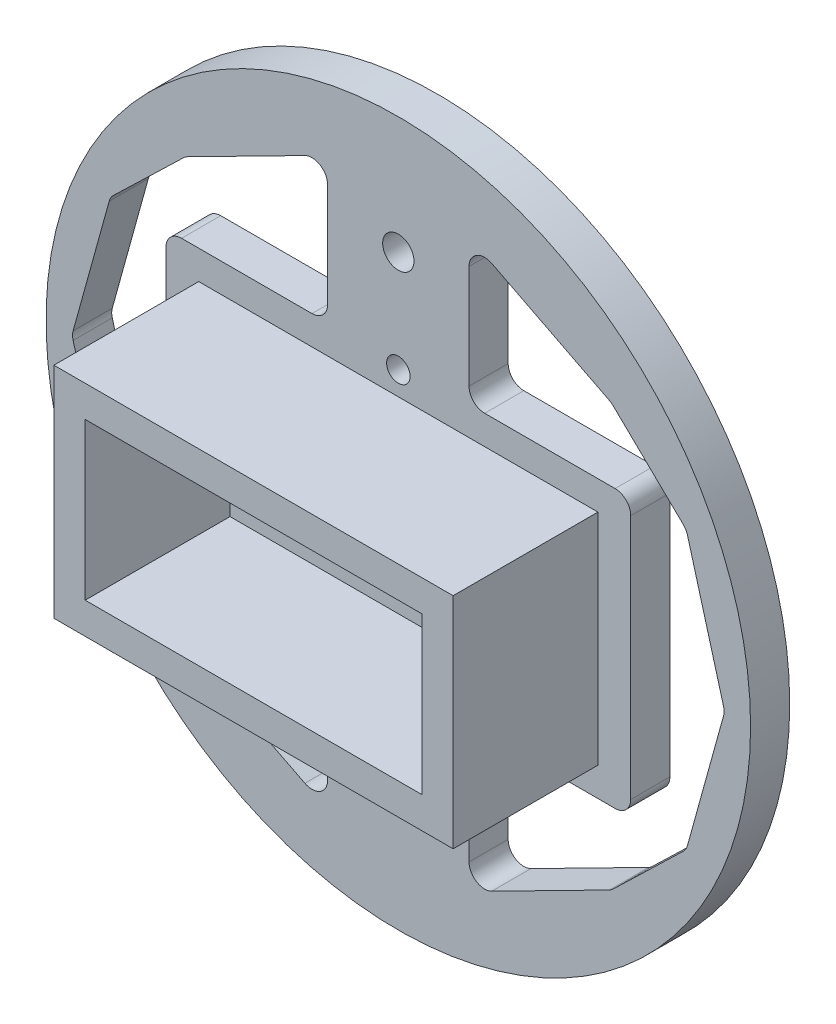
SolidWorks part; units mm, degrees
ref_plane "Front Plane" through (0, 0, 0) normal (0, 0, 1) x (1, 0, 0)
ref_plane "Top Plane" through (0, 0, 0) normal (0, 1, 0) x (1, 0, 0)
ref_plane "Right Plane" through (0, 0, 0) normal (1, 0, 0) x (0, 0, -1)
sketch "Sketch1" plane through (0, 0, 0) normal (0, 0, 1) x (1, 0, 0)
  line L0 (0, 57.2553) -> (0, -57.7928) construction
  line L1 (-56.6552, 0) -> (66.2483, 0) construction
  circle A0 centre (0, 0) radius 45
  circle A1 centre (0, 0) radius 2.5
  circle A2 centre (0, 17) radius 1.5
  circle A3 centre (17, 0) radius 1.5
  circle A4 centre (0, -17) radius 1.5
  circle A5 centre (-17, 0) radius 1.5
  point P19 (0, 0)
  dimension "D1" = 90
  dimension "D2" = 4
  dimension "D3" = 3
  dimension "D4" = 5
extrude "Boss-Extrude1" add sketch "Sketch1" along normal blind 5
sketch "Sketch2" plane through (0, 0, 5) normal (0, 0, 1) x (1, 0, 0)
  line L0 (0, 45) -> (0, -45) construction
  line L1 (-45, 0) -> (45, 0) construction
  line L4 (-25.5, 10) -> (-25.5, -10)
  line L6 (-21.5, 10) -> (-21.5, -10)
  line L7 (-21.5, 10) -> (0, 10)
  line L8 (-25.5, 10) -> (-25.5, 14)
  line L9 (-25.5, 14) -> (0, 14)
  line L10 (0, 10) -> (0, 14)
  line L11 (-21.5, -10) -> (0, -10)
  line L12 (-25.5, -10) -> (-25.5, -14)
  line L13 (-25.5, -14) -> (0, -14)
  line L14 (0, -10) -> (0, -14)
  circle A0 centre (0, 0) radius 45 construction
  circle A1 centre (0, -17) radius 1.5 construction
  point P11 (-25.5, 0)
  dimension "D1" = 21.5
  dimension "D2" = 4
  dimension "D3" = 20
  dimension "D4" = 25.5
extrude "Boss-Extrude2" add sketch "Sketch2" along normal blind 18.5
mirror "Mirror1" about plane through (0, 0, 0) normal (1, 0, 0) of "Boss-Extrude2"
sketch "Sketch4" plane through (0, 0, 5) normal (0, 0, 1) x (1, 0, 0)
  line L0 (-45, 0) -> (45, 0) construction
  circle A0 centre (0, 30) radius 2
  circle A1 centre (0, 0) radius 45 construction
  circle A2 centre (0, -30) radius 2
  dimension "D1" = 4
  dimension "D2" = 30
extrude "Cut-Extrude1" cut sketch "Sketch4" against normal blind 10
sketch "Sketch5" plane through (0, 0, 5) normal (0, 0, 1) x (1, 0, 0)
  line L0 (-29.6896, 17.695) -> (-9.0318, 17.695)
  line L1 (-9.0318, 17.695) -> (-9.0318, 36.201)
  line L2 (-9.0318, 36.201) -> (-27.215, 26.948)
  line L3 (-27.215, 26.948) -> (-36.7908, 17.695)
  line L4 (-36.7908, 17.695) -> (-41.6896, 0)
  line L5 (-41.6896, 0) -> (-29.6896, 0)
  line L6 (-29.6896, -17.695) -> (-29.6896, 17.695)
  line L7 (-12.6899, 0) -> (11.9488, 0) construction
  line L8 (0, 7.5813) -> (0, -6.5134) construction
  line L11 (25.5, 14) -> (25.5, -14) construction
  line L12 (-25.5, -14) -> (25.5, -14) construction
  line L13 (-36.7908, -17.695) -> (-41.6896, 0)
  line L14 (-27.215, -26.948) -> (-36.7908, -17.695)
  line L15 (-9.0318, -36.201) -> (-27.215, -26.948)
  line L16 (-9.0318, -17.695) -> (-9.0318, -36.201)
  line L17 (-29.6896, -17.695) -> (-9.0318, -17.695)
  line L18 (29.6896, -17.695) -> (9.0318, -17.695)
  line L19 (9.0318, -17.695) -> (9.0318, -36.201)
  line L20 (9.0318, -36.201) -> (27.215, -26.948)
  line L21 (27.215, -26.948) -> (36.7908, -17.695)
  line L22 (36.7908, -17.695) -> (41.6896, 0)
  line L23 (29.6896, -17.695) -> (29.6896, 17.695)
  line L24 (41.6896, 0) -> (29.6896, 0)
  line L25 (36.7908, 17.695) -> (41.6896, 0)
  line L26 (27.215, 26.948) -> (36.7908, 17.695)
  line L27 (9.0318, 36.201) -> (27.215, 26.948)
  line L28 (9.0318, 17.695) -> (9.0318, 36.201)
  line L29 (29.6896, 17.695) -> (9.0318, 17.695)
  dimension "D1" = 12
  dimension "D2" = 29.6896
  dimension "D3" = 34.5318
  dimension "D4" = 52.715
  dimension "D5" = 62.2908
  dimension "D6" = 28
  dimension "D7" = 31.695
  dimension "D8" = 40.948
  dimension "D9" = 50.201
extrude "Cut-Extrude2" cut sketch "Sketch5" against normal blind 10 contours L29 L23 L24 L25 L26 L27 L28 | L22 L24 L23 L18 L19 L20 L21 | L17 L6 L5 L13 L14 L15 L16 | L5 L6 L0 L1 L2 L3 L4
fillet "Fillet1" radius 2 22 edges at (29.6896, -17.695, 2.5) (9.0318, 36.201, 2.5) (9.0318, 17.695, 2.5) (29.6896, 17.695, 2.5) (27.215, 26.948, 2.5) (36.7908, 17.695, 2.5) (41.6896, 0, 2.5) (36.7908, -17.695, 2.5) (27.215, -26.948, 2.5) (9.0318, -36.201, 2.5) (9.0318, -17.695, 2.5) (-9.0318, -36.201, 2.5) (-9.0318, -17.695, 2.5) (-27.215, -26.948, 2.5) (-36.7908, -17.695, 2.5) (-29.6896, -17.695, 2.5) (-41.6896, 0, 2.5) (-36.7908, 17.695, 2.5) (-29.6896, 17.695, 2.5) (-9.0318, 17.695, 2.5) (-27.215, 26.948, 2.5) (-9.0318, 36.201, 2.5)
equation "\"filetradius\"= 2mm"
